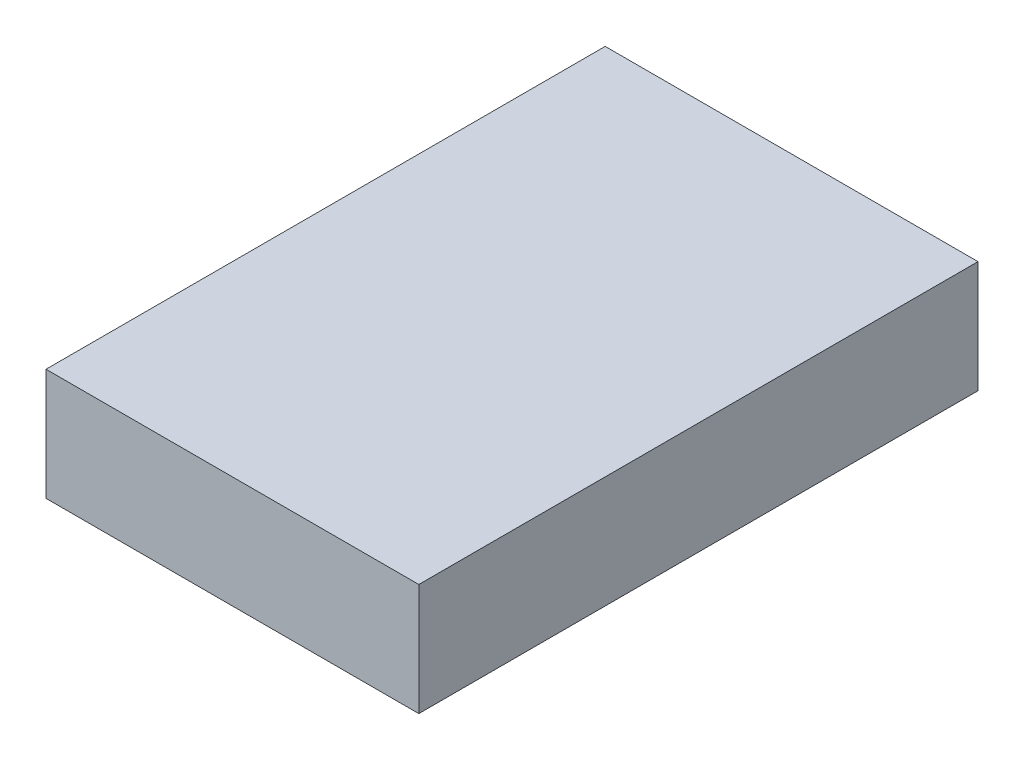
SolidWorks part; units mm, degrees
ref_plane "Front Plane" through (0, 0, 0) normal (0, 0, 1) x (1, 0, 0)
ref_plane "Top Plane" through (0, 0, 0) normal (0, 1, 0) x (1, 0, 0)
ref_plane "Right Plane" through (0, 0, 0) normal (1, 0, 0) x (0, 0, -1)
sketch "Sketch2" plane through (0, 0, 0) normal (0, 1, 0) x (1, 0, 0)
  line L1 (-254, -381) -> (254, -381)
  line L2 (-254, -381) -> (-254, 381)
  line L3 (-254, 381) -> (254, 381)
  line L4 (254, -381) -> (254, 381)
  line L5 (0, 381) -> (0, -381) construction
  line L6 (-254, 0) -> (254, 0) construction
  point P0 (0, 0)
  dimension "D1" = 508
  dimension "D2" = 762
extrude "Boss-Extrude1" add sketch "Sketch2" along normal blind 152.4
